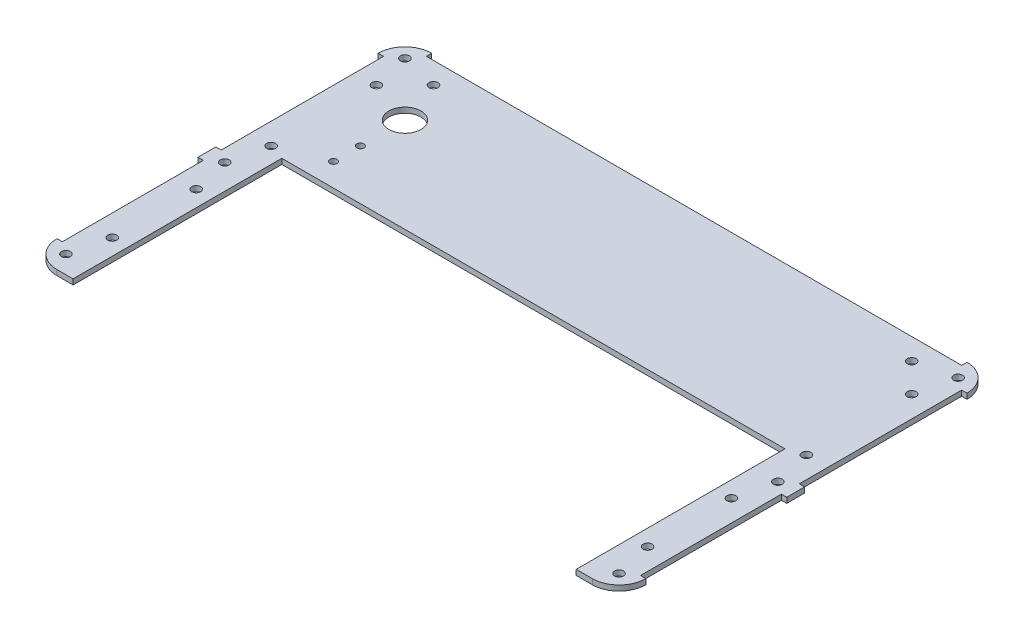
SolidWorks part; units mm, degrees
ref_plane "Plan de face" through (0, 0, 0) normal (0, 0, 1) x (1, 0, 0)
ref_plane "Plan de dessus" through (0, 0, 0) normal (0, 1, 0) x (1, 0, 0)
ref_plane "Plan de droite" through (0, 0, 0) normal (1, 0, 0) x (0, 0, -1)
sketch "Esquisse1" plane through (0, 0, 0) normal (0, 1, 0) x (1, 0, 0)
  line L0 (0, 200) -> (330, 200) construction
  line L1 (0, 0) -> (24, 0)
  line L2 (0, 0) -> (0, 210)
  line L3 (0, 210) -> (330, 210)
  line L4 (330, 0) -> (330, 210)
  line L5 (40, 210) -> (40, 136.5882) construction
  line L6 (165, 210) -> (165, 0) construction
  line L7 (10, 210) -> (10, 0) construction
  line L8 (24, 0) -> (24, 117)
  line L9 (24, 117) -> (165, 117)
  line L10 (0, 0) -> (330, 0) construction
  line L11 (306, 0) -> (306, 117)
  line L12 (330, 0) -> (306, 0)
  line L24 (306, 117) -> (165, 117)
  circle A0 centre (10, 200) radius 2.5
  circle A1 centre (320, 200) radius 2.5
  circle A2 centre (10, 99) radius 2.5
  circle A3 centre (320, 99) radius 2.5
  circle A4 centre (10, 10) radius 2.5
  circle A5 centre (320, 10) radius 2.5
  circle A6 centre (40, 170) radius 9
  circle A7 centre (40, 145) radius 2
  circle A8 centre (40, 130) radius 2
  point P13 (10, 200)
  dimension "D3" = 5
  dimension "D12" = 5
  dimension "D8" = 18
  dimension "D9" = 40
  dimension "D10" = 40
  dimension "D11" = 4
  dimension "D1" = 330
  dimension "D2" = 210
  dimension "D4" = 10
  dimension "D5" = 10
  dimension "D6" = 14
  dimension "D7" = 117
  dimension "D13" = 101
  dimension "D14" = 15
  dimension "D15" = 25
  dimension "D16" = 89
extrude "Extrusion1" add sketch "Esquisse1" along normal blind 3
fillet "Congé1" radius 15 4 edges at (0, 1.5, 0) (330, 1.5, 0) (330, 1.5, -210) (0, 1.5, -210)
sketch "Esquisse2" plane through (0, 3, 0) normal (0, 1, 0) x (1, 0, 0)
  line L0 (165, 210) -> (165, 117) construction
  line L1 (315, 210) -> (15, 210) construction
  line L2 (24, 117) -> (306, 117) construction
  line L3 (15, 210) -> (15, 207)
  line L4 (15, 207) -> (315, 207)
  line L5 (15, 210) -> (315, 210)
  line L6 (0, 195) -> (3, 195)
  line L7 (3, 195) -> (3, 104)
  line L8 (3, 104) -> (0, 104)
  line L9 (0, 195) -> (0, 15) construction
  line L10 (0, 104) -> (0, 195)
  line L11 (0, 15) -> (3, 15)
  line L12 (3, 15) -> (3, 94)
  line L13 (3, 94) -> (0, 94)
  line L14 (10, 99) -> (0, 99) construction
  line L15 (320, 99) -> (330, 99) construction
  line L16 (327, 94) -> (330, 94)
  line L17 (327, 15) -> (327, 94)
  line L18 (330, 15) -> (327, 15)
  line L19 (330, 104) -> (330, 195)
  line L20 (327, 104) -> (330, 104)
  line L21 (327, 195) -> (327, 104)
  line L22 (330, 195) -> (327, 195)
  line L23 (315, 210) -> (315, 207)
  line L24 (0, 94) -> (0, 15)
  line L25 (330, 94) -> (330, 15)
  point P39 (165, 207)
  dimension "D1" = 3
  dimension "D2" = 3
  dimension "D3" = 5
  dimension "D4" = 5
extrude "Extrusion2" cut sketch "Esquisse2" against normal up to next
sketch "Esquisse3" plane through (0, 3, 0) normal (0, 1, 0) x (1, 0, 0)
  line L0 (165, 207) -> (165, 117) construction
  line L1 (15, 207) -> (315, 207) construction
  line L2 (24, 117) -> (306, 117) construction
  line L3 (3, 104) -> (3, 195) construction
  line L4 (15, 179) -> (15, -20.9209) construction
  line L8 (3, 94) -> (0, 94) construction
  line L9 (0, 104) -> (3, 104) construction
  line L10 (0, 15) -> (3, 15) construction
  circle A0 centre (31, 195) radius 2.5
  circle A1 centre (15, 179) radius 2.5
  circle A2 centre (15, 120) radius 2.5
  circle A3 centre (15, 78) radius 2.5
  circle A4 centre (15, 31) radius 2.5
  circle A5 centre (299, 195) radius 2.5
  circle A6 centre (315, 179) radius 2.5
  circle A7 centre (315, 120) radius 2.5
  circle A8 centre (315, 78) radius 2.5
  circle A9 centre (315, 31) radius 2.5
  dimension "D1" = 12
  dimension "D2" = 28
  dimension "D3" = 5
  dimension "D4" = 12
  dimension "D5" = 28
  dimension "D6" = 16
  dimension "D7" = 16
  dimension "D8" = 16
extrude "Extrusion3" cut sketch "Esquisse3" against normal up to next
